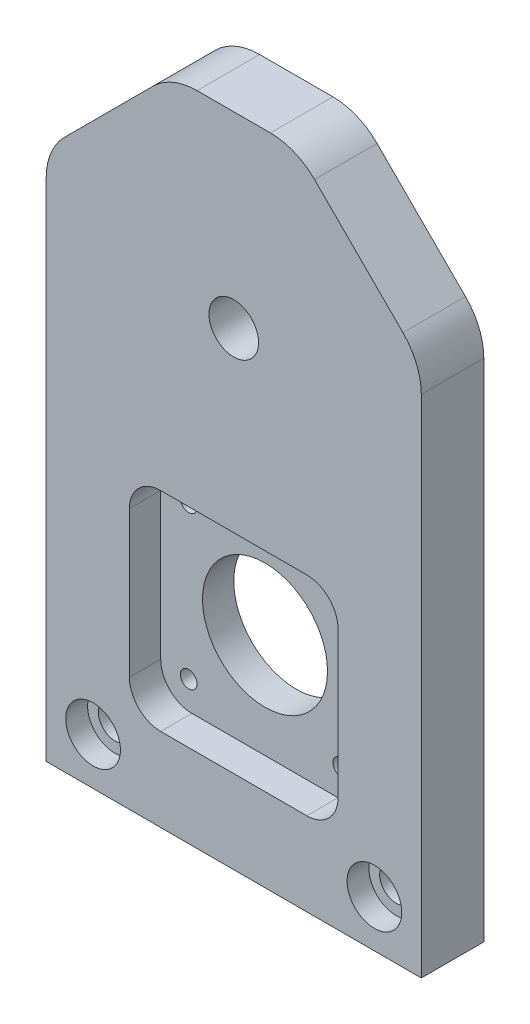
SolidWorks part; units mm, degrees
material "ABS"
ref_plane "Front Plane" through (0, 0, 0) normal (0, 0, 1) x (1, 0, 0)
ref_plane "Top Plane" through (0, 0, 0) normal (0, 1, 0) x (1, 0, 0)
ref_plane "Right Plane" through (0, 0, 0) normal (1, 0, 0) x (0, 0, -1)
sketch "Pitch Circles" plane through (0, 0, 0) normal (0, 0, 1) x (1, 0, 0)
  line L0 (0, 0) -> (-25.4, 25.4) construction
  circle A0 centre (0, 0) radius 44.45 construction
  circle A1 centre (0, -57.15) radius 12.7 construction
  dimension "D3" = 88.9
  dimension "D4" = 25.4
  dimension "D1" = 25.4
  dimension "D2" = 25.4
sketch "Sketch2" plane through (0, 0, 0) normal (0, 0, 1) x (1, 0, 0)
  line L0 (0, 0) -> (38.1, 0) construction
  line L1 (-38.1, -95.25) -> (38.1, -95.25)
  line L2 (-38.1, -95.25) -> (-38.1, 38.1)
  line L3 (-38.1, 38.1) -> (38.1, 38.1)
  line L4 (38.1, -95.25) -> (38.1, 38.1)
  line L5 (-38.1, -95.25) -> (38.1, 38.1) construction
  line L6 (-38.1, 38.1) -> (38.1, -95.25) construction
  line L7 (0, 0) -> (0, 38.1) construction
  point P0 (0, -28.575)
  dimension "D1" = 76.2
  dimension "D2" = 133.35
extrude "Boss-Extrude1" add sketch "Sketch2" along normal mid plane 12.7
hole_wizard "3/8 Clearance Hole1" positions "Sketch3" profile "Sketch4" hole size "3/8" standard "ANSI Inch" end condition through all
sketch "Sketch3" plane through (0, 0, 6.35) normal (0, 0, 1) x (1, 0, 0)
  point P0 (0, 0)
sketch "Sketch4" plane through (0, 0, 6.35) normal (1, 0, 0) x (0, -1, 0)
  line L0 (0, 0) -> (0, 12.7)
  line L1 (0, 12.7) -> (5.0419, 12.7)
  line L2 (5.0419, 12.7) -> (5.0419, 0)
  line L5 (5.0419, 0) -> (0, 0)
  line L11 (0, -6.35) -> (0, 107.95) construction
  dimension "Thru Hole Dia." = 10.0838
  dimension "Thru Hole Depth" = 12.7
sketch "Sketch5" plane through (0, 0, 0) normal (0, 0, 1) x (1, 0, 0)
  line L0 (0, -57.15) -> (0, -41.65) construction
  line L1 (-15.5, -72.65) -> (15.5, -72.65)
  line L2 (-15.5, -72.65) -> (-15.5, -41.65)
  line L3 (-15.5, -41.65) -> (15.5, -41.65)
  line L4 (15.5, -72.65) -> (15.5, -41.65)
  line L5 (-15.5, -72.65) -> (15.5, -41.65) construction
  line L6 (-15.5, -41.65) -> (15.5, -72.65) construction
  line L7 (-21, -78.15) -> (21, -78.15)
  line L8 (-21, -78.15) -> (-21, -36.15)
  line L9 (-21, -36.15) -> (21, -36.15)
  line L10 (21, -78.15) -> (21, -36.15)
  line L11 (-21, -78.15) -> (21, -36.15) construction
  line L12 (-21, -36.15) -> (21, -78.15) construction
  point P0 (0, -57.15)
  point P5 (0, -57.15)
  dimension "D1" = 42
  dimension "D2" = 31
sketch "Sketch6" plane through (0, 0, 6.35) normal (0, 0, 1) x (1, 0, 0)
  line L16 (-22.27, -79.42) -> (22.27, -79.42)
  line L17 (22.27, -79.42) -> (22.27, -34.88)
  line L18 (22.27, -34.88) -> (-22.27, -34.88)
  line L19 (-22.27, -34.88) -> (-22.27, -79.42)
  line L20 (-22.27, -79.42) -> (22.27, -79.42)
  line L21 (22.27, -79.42) -> (22.27, -34.88)
  line L22 (22.27, -34.88) -> (-22.27, -34.88)
  line L23 (-22.27, -34.88) -> (-22.27, -79.42)
  dimension "D1" = 1.27
extrude "Cut-Extrude1" [suppressed] cut sketch "Sketch6" against normal blind 9.525
hole_wizard "M3 Clearance Hole1" positions "Sketch7" profile "Sketch8" hole size "M3" standard "ANSI Metric" end condition through all
sketch "Sketch7" plane through (0, 0, 6.35) normal (0, 0, 1) x (1, 0, 0)
  point P0 (-15.5, -41.65)
  point P3 (15.5, -41.65)
  point P6 (15.5, -72.65)
  point P9 (-15.5, -72.65)
sketch "Sketch8" plane through (-15.5, -41.65, 6.35) normal (1, 0, 0) x (0, -1, 0)
  line L0 (0, 0) -> (0, 12.7)
  line L1 (0, 12.7) -> (1.7, 12.7)
  line L2 (1.7, 12.7) -> (1.7, 0)
  line L5 (1.7, 0) -> (0, 0)
  line L11 (0, -6.35) -> (0, 107.95) construction
  dimension "Thru Hole Dia." = 3.4
  dimension "Thru Hole Depth" = 12.7
sketch "Sketch13" plane through (0, 0, 6.35) normal (0, 0, 1) x (1, 0, 0)
  circle A0 centre (0, -57.15) radius 12.7
  dimension "D1" = 25.4
extrude "Cut-Extrude2" cut sketch "Sketch13" against normal through all contours A0
sketch "Sketch14" plane through (0, 0, 6.35) normal (0, 0, 1) x (1, 0, 0)
  line L1 (-21.1905, -78.3405) -> (21.1905, -78.3405)
  line L2 (-21.1905, -78.3405) -> (-21.1905, -35.9595)
  line L3 (-21.1905, -35.9595) -> (21.1905, -35.9595)
  line L4 (21.1905, -78.3405) -> (21.1905, -35.9595)
  line L5 (-21.1905, -78.3405) -> (21.1905, -35.9595) construction
  line L6 (-21.1905, -35.9595) -> (21.1905, -78.3405) construction
  point P0 (0, -57.15)
  dimension "D1" = 42.381
extrude "Cut-Extrude3" cut sketch "Sketch14" against normal offset from surface (6.35 mm away) 6.35 up to face at (12.7, -57.15, -6.35)
chamfer "Chamfer1" distance 25.4 angle 45 2 edges at (38.1, 38.1, 0) (-38.1, 38.1, 0)
sketch "Base Mount Profile" plane through (0, 0, 6.35) normal (0, 0, 1) x (1, 0, 0)
  line L0 (-38.1, -76.2) -> (38.1, -76.2) construction
  line L1 (-38.1, 12.7) -> (-38.1, -95.25) construction
  line L2 (38.1, -95.25) -> (38.1, 12.7) construction
  line L3 (-38.1, -95.25) -> (38.1, -95.25) construction
  dimension "D1" = 19.05
hole_wizard "CBORE for 1/4 Socket Head Cap Screw1" positions "Sketch11" profile "Sketch12" counterbore size "1/4" standard "ANSI Inch" end condition through all
sketch "Sketch11" plane through (0, 0, 6.35) normal (0, 0, 1) x (1, 0, 0)
  line L0 (-28.575, -85.725) -> (28.575, -85.725) construction
  line L2 (0, -85.725) -> (0, -76.2) construction
  line L3 (-38.1, -76.2) -> (38.1, -76.2) construction
  line L6 (0, -85.725) -> (0, -95.25) construction
  line L7 (-38.1, -95.25) -> (38.1, -95.25) construction
  line L8 (-38.1, 12.7) -> (-38.1, -95.25) construction
  point P1 (-28.575, -85.725)
  point P2 (28.575, -85.725)
  point P5 (0, -85.725)
  dimension "D1" = 9.525
sketch "Sketch12" plane through (-28.575, -85.725, 6.35) normal (1, 0, 0) x (0, -1, 0)
  line L0 (0, 0) -> (0, 12.7)
  line L1 (0, 12.7) -> (3.3782, 12.7)
  line L3 (3.3782, 12.7) -> (3.3782, 4.445)
  line L4 (3.3782, 4.445) -> (5.5562, 4.445)
  line L5 (5.5562, 4.445) -> (5.5562, 0)
  line L7 (5.5562, 0) -> (0, 0)
  line L11 (0, -6.35) -> (0, 107.95) construction
  dimension "Thru Hole Dia." = 6.7564
  dimension "Thru Hole Depth" = 12.7
  dimension "C'Bore Dia." = 11.1125
  dimension "C'Bore Depth" = 4.445
hole_wizard "CBORE for M3 SHCS1" positions "Sketch15" profile "Sketch16" counterbore size "M3" standard "ANSI Metric" end condition through all
sketch "Sketch15" plane through (0, 0, -6.35) normal (0, 0, -1) x (-1, 0, 0)
  point P0 (-15.5, -41.65)
  point P3 (15.5, -41.65)
  point P6 (15.5, -72.65)
  point P9 (-15.5, -72.65)
sketch "Sketch16" plane through (15.5, -41.65, -6.35) normal (1, 0, 0) x (0, 1, 0)
  line L0 (0, 0) -> (0, 12.7)
  line L1 (0, 12.7) -> (1.7, 12.7)
  line L3 (1.7, 12.7) -> (1.7, 3)
  line L4 (1.7, 3) -> (3.25, 3)
  line L5 (3.25, 3) -> (3.25, 0)
  line L7 (3.25, 0) -> (0, 0)
  line L11 (0, -6.35) -> (0, 107.95) construction
  dimension "Thru Hole Dia." = 3.4
  dimension "Thru Hole Depth" = 12.7
  dimension "C'Bore Dia." = 6.5
  dimension "C'Bore Depth" = 3
fillet "Fillet1" radius 6.35 4 edges at (21.1905, -78.3405, 3.175) (-21.1905, -35.9595, 3.175) (21.1905, -35.9595, 3.175) (-21.1905, -78.3405, 3.175)
fillet "Fillet2" radius 12.7 4 edges at (38.1, 12.7, 0) (12.7, 38.1, 0) (-12.7, 38.1, 0) (-38.1, 12.7, 0)
equation "\"D1@Sketch14\"=42mm+.015"
